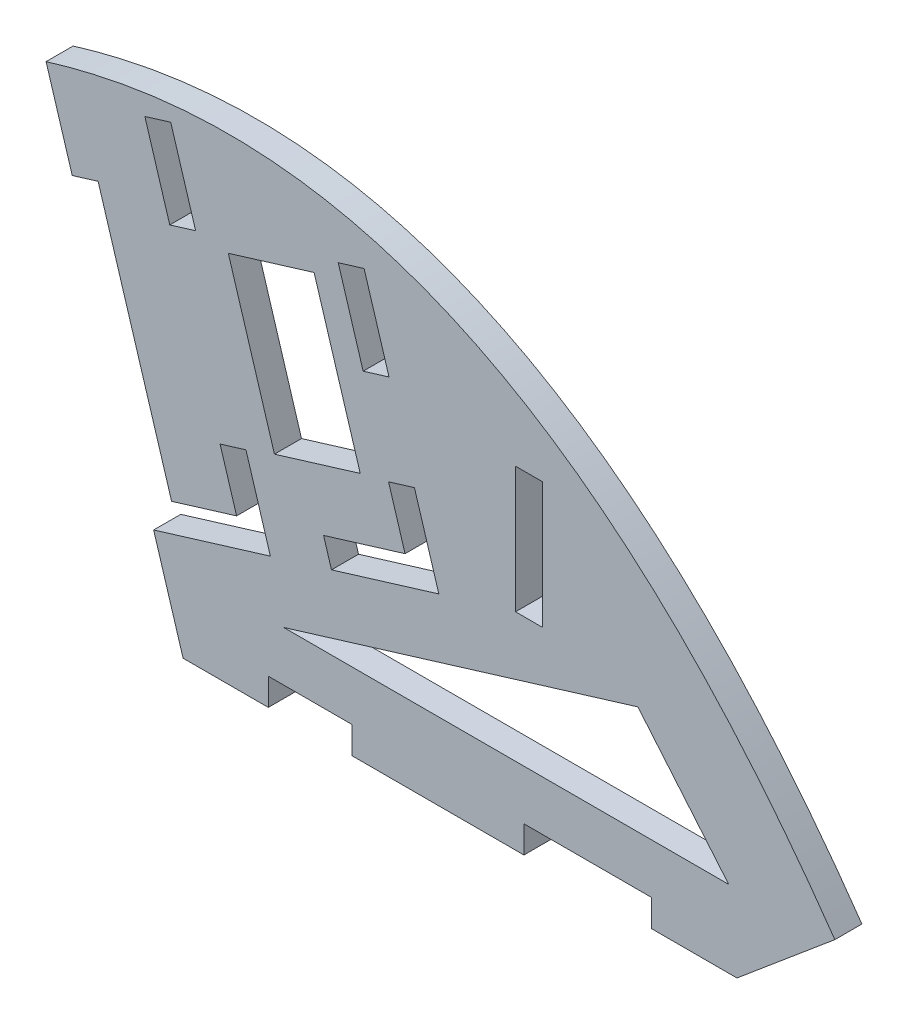
SolidWorks part; units mm, degrees
ref_plane "Front Plane" through (0, 0, 0) normal (0, 0, 1) x (1, 0, 0)
ref_plane "Top Plane" through (0, 0, 0) normal (0, 1, 0) x (1, 0, 0)
ref_plane "Right Plane" through (0, 0, 0) normal (1, 0, 0) x (0, 0, -1)
sketch "Sketch1" plane through (0, 0, 0) normal (0, 0, 1) x (1, 0, 0)
  line L0 (0, 0) -> (65, 0)
  line L1 (0, 0) -> (-16.0804, 52.5968)
  line L2 (65, 0) -> (76.4907, 9.6418)
  line L3 (274.2111, 141.3478) -> (304.597, 150.6377) construction
  spline S0 degree 2 poles (76.4907, 9.6418) (35.6676, 68.4177) (-16.0804, 52.5968) knots 0 0 0 1 1 1
  dimension "D1" = 65
  dimension "D2" = 15
  dimension "D3" = 55
  dimension "D4" = 107
  dimension "D5" = 140
extrude "Boss-Extrude1" add sketch "Sketch1" along normal blind 3.175
sketch "Sketch3" plane through (0, 0, 0) normal (0, 0, -1) x (-1, 0, 0)
  line L0 (-39.0142, 24.227) -> (-39.0142, 39.789) construction
  line L1 (-42.1892, 24.227) -> (-39.0142, 24.227)
  line L2 (-42.1892, 24.227) -> (-42.1892, 39.027)
  line L3 (-42.1892, 39.027) -> (-39.0142, 39.027)
  line L4 (-39.0142, 24.227) -> (-39.0142, 39.027)
  line L5 (-21.2422, 50.2305) -> (-18.206, 49.3022)
  line L6 (-18.206, 49.3022) -> (-21.1297, 39.7391)
  line L7 (-18.206, 49.3022) -> (-21.1297, 39.7391) construction
  line L8 (-21.1297, 39.7391) -> (-24.1659, 40.6674)
  line L9 (-21.2422, 50.2305) -> (-24.1659, 40.6674) construction
  line L10 (-24.1659, 40.6674) -> (-21.2422, 50.2305)
  line L11 (-30.0134, 21.5413) -> (-26.9771, 20.613)
  line L12 (-26.9771, 20.613) -> (-24.1119, 29.9848)
  line L13 (-24.1119, 29.9848) -> (-27.1481, 30.9131)
  line L14 (-27.1481, 30.9131) -> (-30.0134, 21.5413)
  line L15 (-26.9771, 20.613) -> (-26.0488, 23.6493)
  line L16 (-29.0851, 24.5776) -> (4.3856, 14.3446) construction
  line L17 (-26.0488, 23.6493) -> (-16.4858, 20.7256)
  line L18 (-16.4858, 20.7256) -> (-17.4141, 17.6893)
  line L19 (-30.0134, 21.5413) -> (3.4573, 11.3083) construction
  line L20 (-17.4141, 17.6893) -> (-26.9771, 20.613)
  line L21 (3.4573, 11.3083) -> (-7.2055, 14.5682)
  line L22 (-7.2055, 14.5682) -> (-4.3403, 23.94) construction
  line L23 (-7.2055, 14.5682) -> (-6.2772, 17.6045)
  line L24 (-6.2772, 17.6045) -> (4.3856, 14.3446)
  line L25 (16.0804, 52.5968) -> (0, 0) construction
  line L26 (4.3856, 14.3446) -> (3.4573, 11.3083)
  line L27 (1.4531, 53.7487) -> (4.4894, 52.8204)
  line L28 (4.4894, 52.8204) -> (1.5656, 43.2574)
  line L29 (1.5656, 43.2574) -> (-1.4706, 44.1857)
  line L30 (-10.2418, 15.4965) -> (-7.3765, 24.8683) construction
  line L31 (-1.4706, 44.1857) -> (1.4531, 53.7487)
  line L32 (-7.2055, 14.5682) -> (-10.2418, 15.4965)
  line L33 (-10.2418, 15.4965) -> (-7.3765, 24.8683)
  line L34 (-7.3765, 24.8683) -> (-4.3403, 23.94)
  line L35 (-4.3403, 23.94) -> (-7.2055, 14.5682)
  point P41 (-8.7236, 15.0324)
  line M13 (0, 0) -> (16.0804, 52.5968)
  dimension "D1" = 14.8
  dimension "D2" = 10
  dimension "D3" = 9.8
  dimension "D4" = 13.175
  dimension "D5" = 10
  dimension "D6" = 9.8
extrude "Cut-Extrude1" cut sketch "Sketch3" against normal through all contours L1 L4 L3 L2 | L10 L8 L6 L5 | L13 L14 L11 L12 | L20 L18 L17 L12 | L31 L29 L28 L27 | L35 L34 L33 L32 L23 | L24 L23 L21 M13
sketch "Sketch4" plane through (0, 0, 0) normal (0, 0, -1) x (-1, 0, 0)
  line L0 (9.9743, 43.4838) -> (1.3493, 15.2729)
  line L1 (-6.2772, 17.6045) -> (4.3856, 14.3446) construction
  line L2 (0.421, 12.2366) -> (1.3493, 15.2729) construction
  line L3 (1.3493, 15.2729) -> (4.3856, 14.3446)
  line L4 (4.3856, 14.3446) -> (13.0105, 42.5556)
  line L5 (16.0804, 52.5968) -> (4.3856, 14.3446) construction
  line L7 (13.0105, 42.5556) -> (9.9743, 43.4838)
  line L9 (0, 0) -> (-65, 0) construction
  line L10 (-55, 0) -> (-40, 0)
  line L11 (-55, 0) -> (-55, 3.175)
  line L12 (-55, 3.175) -> (-40, 3.175)
  line L13 (-40, 0) -> (-40, 3.175)
  line L14 (-55, 3.175) -> (-55, 0) construction
  line L15 (-10, 3.175) -> (-10, 0) construction
  line L16 (-19.8, 3.175) -> (-10, 3.175)
  line L17 (-19.8, 3.175) -> (-19.8, 0)
  line L18 (-19.8, 0) -> (-10, 0)
  line L19 (-10, 3.175) -> (-10, 0)
  line M12 (-6.2772, 17.6045) -> (4.3856, 14.3446)
  line M13 (4.3856, 14.3446) -> (16.0804, 52.5968)
  line M16 (-65, 0) -> (0, 0)
  dimension "D1" = 29.5
  dimension "D2" = 9.8
  dimension "D3" = 3.175
extrude "Cut-Extrude2" cut sketch "Sketch4" against normal blind 3.175 contours L19 L16 L17 M16 | L13 L12 L11 M16 | L7 L0 M13 M12
sketch "Sketch5" plane through (0, 0, 3.175) normal (0, 0, 1) x (1, 0, 0)
  line L38 (11.8043, 9.0309) -> (53.3712, 21.7392)
  line L39 (53.3712, 21.7392) -> (64.0348, 9.0309)
  line L40 (64.0348, 9.0309) -> (11.8043, 9.0309)
  line L41 (5.306, 43.812) -> (10.7211, 26.1)
  line L42 (10.7211, 26.1) -> (20.79, 29.1784)
  line L43 (20.79, 29.1784) -> (15.3749, 46.8903)
  line L44 (15.3749, 46.8903) -> (5.306, 43.812)
extrude "Cut-Extrude3" cut sketch "Sketch5" against normal through all
